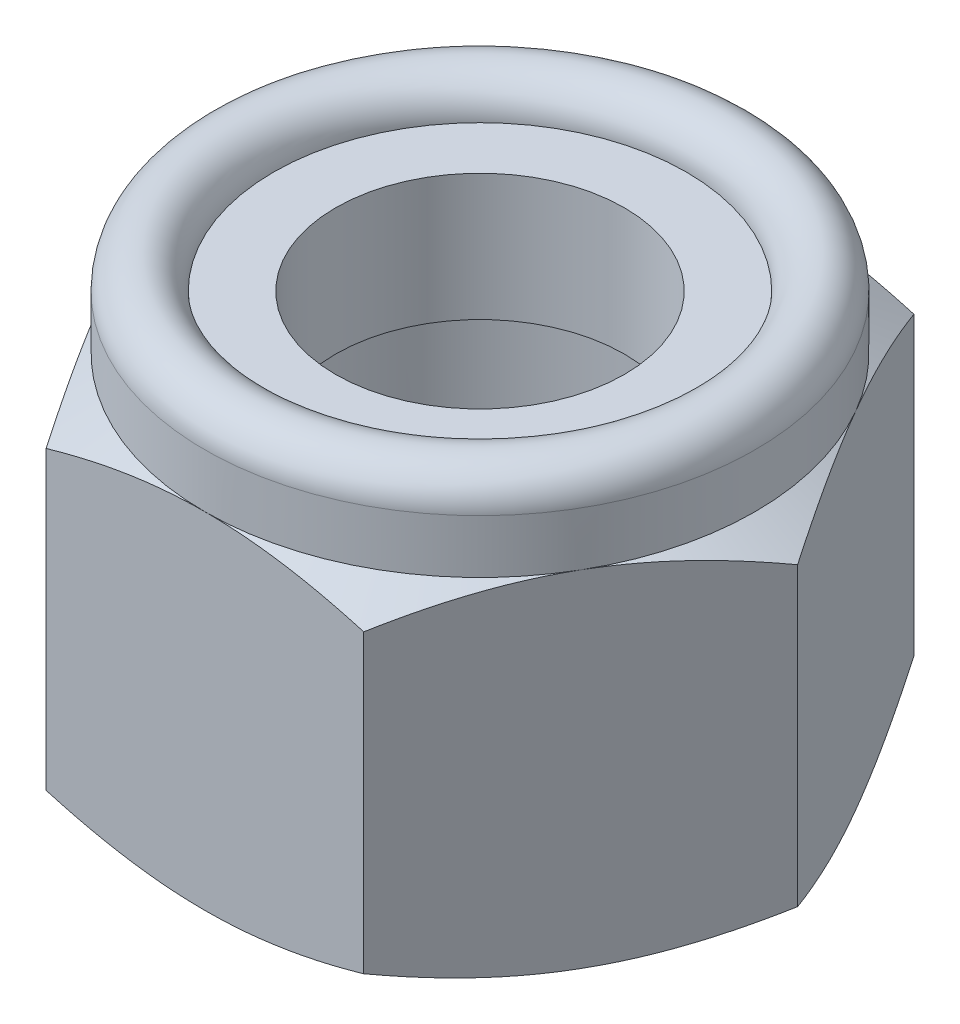
SolidWorks part; units mm, degrees
ref_plane "Face" through (0, 0, 0) normal (0, 0, 1) x (1, 0, 0)
ref_plane "Dessus" through (0, 0, 0) normal (0, 1, 0) x (1, 0, 0)
ref_plane "Droite" through (0, 0, 0) normal (1, 0, 0) x (0, 0, -1)
sketch "Esquisse1" plane through (0, 0, 0) normal (0, 0, 1) x (1, 0, 0)
  line L1 (0, 6.3) -> (4.9778, 6.3) construction
  line L2 (3, 5.8) -> (3.5, 5.8)
  line L3 (5.6569, 4.0645) -> (5.6569, 0.9566)
  line L4 (5.6569, 0.9566) -> (4, 0)
  line L5 (2.5, 4.0645) -> (2.5, 0)
  line L7 (2.5, 0) -> (4, 0)
  line L8 (2.5, 4.0645) -> (3.5, 4.3325)
  line L9 (5.6569, 4.0645) -> (4, 5.0211)
  line L10 (4, 5.0211) -> (4, 5.8)
  line L11 (-2.5, 0) -> (2.5, 0) construction
  line L12 (-4, 0) -> (4, 0) construction
  line L13 (0, 0) -> (0, 6.3) construction
  line L15 (3.5, 5.8) -> (3.5, 4.3325)
  arc A0 (4, 5.8) -> (3, 5.8) centre (3.5, 5.8) ccw
  dimension "D2" = 105
  dimension "D7" = 30
  dimension "D9" = 3
  dimension "D1" = 5.6569
  dimension "Hauteur" = 6.3
  dimension "D3" = 2.5
  dimension "D4" = 4
  dimension "D5" = 4.0645
  dimension "D6" = 60
  dimension "Cote sur plats" = 8
  dimension "Diamètre nominal" = 5
revolve "Base-Révolution" add sketch "Esquisse1" angle 360 about L13
sketch "Esquisse2" plane through (0, 0, 0) normal (0, 1, 0) x (1, 0, 0)
  line L0 (0, 0) -> (0, 4) construction
  line L1 (0, 0) -> (5.6569, 0) construction
  line L2 (0, 0) -> (2.8284, 4.899) construction
  line L3 (0, 0) -> (4.899, 2.8284) construction
  line L4 (-2.3094, 4) -> (2.3094, 4)
  line L5 (2.3094, 4) -> (4.6188, 0)
  line L6 (2.3094, -4) -> (4.6188, 0)
  line L7 (-2.3094, -4) -> (2.3094, -4)
  line L8 (-2.3094, 4) -> (-4.6188, 0)
  line L9 (-2.3094, -4) -> (-4.6188, 0)
  circle A0 centre (0, 0) radius 4 construction
  circle A1 centre (0, 0) radius 5.6569 construction
  point P16 (0, -4)
  dimension "D1" = 30
  dimension "D2" = 30
extrude "Enlèv. mat.-Extru.2" cut sketch "Esquisse2" along normal through all flip side to cut
sketch "Esquisse4" plane through (0, 0, 0) normal (0, 0, 1) x (1, 0, 0)
  line L0 (0, 5.0211) -> (0, -0.0698) construction
  line L1 (2.1, 3.9573) -> (2.1, 5.8)
  line L2 (2.1, 5.8) -> (3.5, 5.8)
  line L3 (3.4641, 5.0211) -> (0, 5.0211) construction
  line L4 (-3.5, 5.8) -> (3.5, 5.8) construction
  line L13 (3.5, 4.3325) -> (3.5, 5.8) construction
  line L16 (3.5, 5.8) -> (3.5, 4.3325)
  line L17 (3.5, 4.3325) -> (2.1, 3.9573)
  line L19 (2.5, 4.0645) -> (3.5, 4.3325) construction
  dimension "D1" = 4.2
revolve "Boss.-Révol.1" add sketch "Esquisse4" angle 360 about L0
equation "\"D3@Esquisse1\" = \"Diamètre nominal@Esquisse1\"/2"
equation "\"D4@Esquisse1\" = \"Cote sur plats@Esquisse1\"/2"
equation "\"D1@Esquisse1\" = \"D4@Esquisse1\"/sqr(2)*2"
equation "\"D9@Esquisse1\" = \"D3@Esquisse1\"+(\"D3@Esquisse1\"*0.2)"
equation "\"D5@Esquisse1\" = \"Hauteur@Esquisse1\"/1.55"
